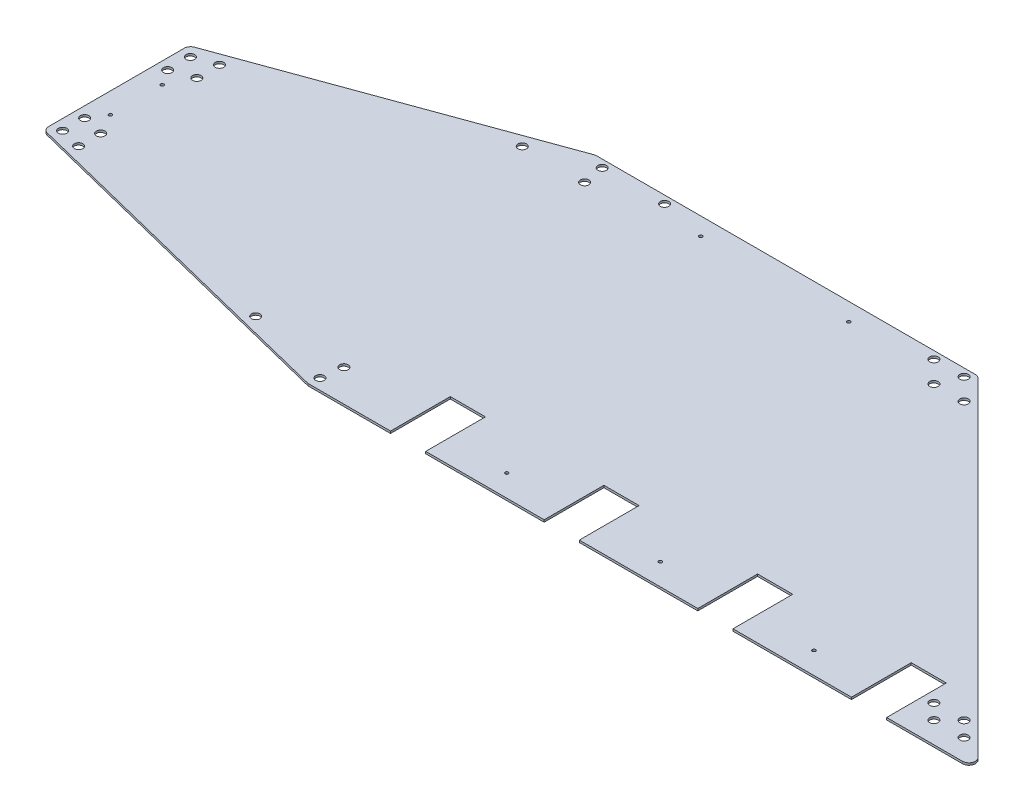
SolidWorks part; units mm, degrees
material "PC High Viscosity"
ref_plane "Front Plane" through (0, 0, 0) normal (0, 0, 1) x (1, 0, 0)
ref_plane "Top Plane" through (0, 0, 0) normal (0, 1, 0) x (1, 0, 0)
ref_plane "Right Plane" through (0, 0, 0) normal (1, 0, 0) x (0, 0, -1)
sketch "Sketch2" plane through (0, 0, 0) normal (0, 1, 0) x (1, 0, 0)
  line L5 (993.5568, 0) -> (0.4168, 0) construction
  line L6 (-516.6797, 128.8227) -> (-1.1348, 0.2829)
  line L7 (1.1695, 0) -> (973.9292, 0)
  line L8 (491.7144, 505.2102) -> (980.6644, 16.2602)
  line L9 (-78.5666, 508) -> (484.9792, 508)
  line L10 (-81.8243, 507.4256) -> (-517.6331, 348.8041)
  line L11 (-523.9004, 339.8536) -> (-523.9004, 138.0648)
  line L36 (122.8448, 0) -> (122.8448, 88.9)
  line L37 (122.8448, 88.9) -> (175.1688, 88.9)
  line L38 (175.1688, 0) -> (175.1688, 88.9)
  line L49 (351.4448, 0) -> (351.4448, 88.9)
  line L50 (351.4448, 88.9) -> (403.7688, 88.9)
  line L51 (403.7688, 0) -> (403.7688, 88.9)
  line L57 (580.0448, 0) -> (580.0448, 88.9)
  line L58 (580.0448, 88.9) -> (632.3688, 88.9)
  line L59 (632.3688, 0) -> (632.3688, 88.9)
  line L61 (808.6448, 0) -> (808.6448, 88.9)
  line L62 (808.6448, 88.9) -> (860.9688, 88.9)
  line L63 (860.9688, 0) -> (860.9688, 88.9)
  arc A0 (-517.6331, 348.8041) -> (-523.9004, 339.8536) centre (-514.3754, 339.8536) ccw
  arc A1 (-523.9004, 138.0648) -> (-516.6797, 128.8227) centre (-514.3754, 138.0648) ccw
  arc A2 (-1.1348, 0.2829) -> (1.1695, 0) centre (1.1695, 9.525) ccw
  arc A3 (980.6644, 16.2602) -> (973.9292, 0) centre (973.9292, 9.525) cw
  arc A4 (491.7144, 505.2102) -> (484.9792, 508) centre (484.9792, 498.475) ccw
  arc A5 (-81.8243, 507.4256) -> (-78.5666, 508) centre (-78.5666, 498.475) cw
  circle A6 centre (133.2169, 15.875) radius 7.62
  circle A7 centre (5.8746, 47.625) radius 6.35
  circle A8 centre (1.9762, 15.875) radius 6.35
  circle A9 centre (-125.3661, 47.625) radius 6.35
  circle A10 centre (-508.0254, 175.7547) radius 6.35
  circle A11 centre (-508.0254, 143.0327) radius 6.35
  circle A12 centre (-476.2754, 167.8385) radius 6.35
  circle A13 centre (-476.2754, 135.1165) radius 6.35
  circle A14 centre (-508.0254, 333.1213) radius 6.35
  circle A15 centre (-476.2754, 344.6773) radius 6.35
  circle A16 centre (-476.2754, 310.8897) radius 6.35
  circle A17 centre (-508.0254, 299.3336) radius 6.35
  circle A18 centre (-146.0386, 464.8731) radius 6.35
  circle A19 centre (-58.8062, 496.6231) radius 6.35
  circle A20 centre (-53.2079, 464.8731) radius 6.35
  circle A21 centre (34.0246, 496.6231) radius 6.35
  circle A22 centre (434.692, 496.623) radius 6.35
  circle A23 centre (466.4419, 464.873) radius 6.35
  circle A24 centre (479.5932, 496.623) radius 6.35
  circle A25 centre (511.3432, 464.873) radius 6.35
  circle A26 centre (877.3398, 53.975) radius 6.35
  circle A27 centre (922.2411, 53.975) radius 6.35
  circle A28 centre (899.5648, 31.75) radius 6.35
  circle A29 centre (944.4661, 31.75) radius 6.35
  circle A31 centre (322.9287, 481.637) radius 2.4575
  circle A32 centre (263.3068, 32.385) radius 2.4575
  circle A33 centre (491.9068, 32.385) radius 2.4575
  circle A34 centre (720.5068, 32.385) radius 2.4575
  circle A35 centre (-493.0394, 276.2907) radius 2.4574
  circle A36 centre (-493.0394, 199.0909) radius 2.4574
  circle A37 centre (102.7505, 481.637) radius 2.4575
  point P8 (-523.9004, 346.523)
  point P18 (-523.9004, 130.623)
  point P21 (0, 0)
  point P24 (996.9246, 0)
  dimension "D9" = 9.525
  dimension "D11" = 121.6753
  dimension "D12" = 52.324
  dimension "D13" = 176.276
  dimension "D14" = 176.276
  dimension "D15" = 176.276
  dimension "D16" = 220.1782
  dimension "D39" = 12.7
  dimension "D45" = 15.24
  dimension "D35" = 4.9149
  dimension "D51" = 4.9149
  dimension "D53" = 4.9149
  dimension "D1" = 523.9004
  dimension "D2" = 508
  dimension "D3" = 1520.825
  dimension "D4" = 166
  dimension "D5" = 160
  dimension "D6" = 110
  dimension "D7" = 215.9
  dimension "D8" = 45
  dimension "D10" = 531.3276
  dimension "D24" = 88.9
  dimension "D25" = 199.0909
  dimension "D29" = 77.1998
  dimension "D30" = 88.9
  dimension "D31" = 88.9
  dimension "D32" = 88.9
extrude "Boss-Extrude1" add sketch "Sketch2" along normal blind 3.175
fillet "Fillet1" [suppressed] radius 3.175
sketch "Sketch6" plane through (0, 3.175, 0) normal (0, 1, 0) x (1, 0, 0)
  line L0 (-22.6592, 431.8127) -> (-22.6592, 406.4127) construction
  line L1 (-9.9592, 431.8127) -> (-9.9592, 406.4127)
  line L2 (-35.3592, 431.8127) -> (-35.3592, 406.4127)
  line L3 (-102.0342, 431.8127) -> (-102.0342, 406.4127) construction
  line L4 (-89.3342, 431.8127) -> (-89.3342, 406.4127)
  line L5 (-114.7342, 431.8127) -> (-114.7342, 406.4127)
  line L6 (-22.6592, 273.0627) -> (-22.6592, 247.6627) construction
  line L7 (-9.9592, 273.0627) -> (-9.9592, 247.6627)
  line L8 (-35.3592, 273.0627) -> (-35.3592, 247.6627)
  line L9 (-102.0342, 273.0627) -> (-102.0342, 247.6627) construction
  line L10 (-89.3342, 273.0627) -> (-89.3342, 247.6627)
  line L11 (-114.7342, 273.0627) -> (-114.7342, 247.6627)
  line L12 (-22.6592, 114.3127) -> (-22.6592, 88.9127) construction
  line L13 (-9.9592, 114.3127) -> (-9.9592, 88.9127)
  line L14 (-35.3592, 114.3127) -> (-35.3592, 88.9127)
  line L15 (-102.0342, 114.3127) -> (-102.0342, 88.9127) construction
  line L16 (-89.3342, 114.3127) -> (-89.3342, 88.9127)
  line L17 (-114.7342, 114.3127) -> (-114.7342, 88.9127)
  arc A0 (-9.9592, 431.8127) -> (-35.3592, 431.8127) centre (-22.6592, 431.8127) ccw
  arc A1 (-35.3592, 406.4127) -> (-9.9592, 406.4127) centre (-22.6592, 406.4127) ccw
  arc A2 (-89.3342, 431.8127) -> (-114.7342, 431.8127) centre (-102.0342, 431.8127) ccw
  arc A3 (-114.7342, 406.4127) -> (-89.3342, 406.4127) centre (-102.0342, 406.4127) ccw
  arc A4 (-9.9592, 273.0627) -> (-35.3592, 273.0627) centre (-22.6592, 273.0627) ccw
  arc A5 (-35.3592, 247.6627) -> (-9.9592, 247.6627) centre (-22.6592, 247.6627) ccw
  arc A6 (-89.3342, 273.0627) -> (-114.7342, 273.0627) centre (-102.0342, 273.0627) ccw
  arc A7 (-114.7342, 247.6627) -> (-89.3342, 247.6627) centre (-102.0342, 247.6627) ccw
  arc A8 (-9.9592, 114.3127) -> (-35.3592, 114.3127) centre (-22.6592, 114.3127) ccw
  arc A9 (-35.3592, 88.9127) -> (-9.9592, 88.9127) centre (-22.6592, 88.9127) ccw
  arc A10 (-89.3342, 114.3127) -> (-114.7342, 114.3127) centre (-102.0342, 114.3127) ccw
  arc A11 (-114.7342, 88.9127) -> (-89.3342, 88.9127) centre (-102.0342, 88.9127) ccw
  point P1 (-76.6342, 419.1127)
  point P2 (-48.0592, 260.3627)
  point P3 (-76.6342, 260.3627)
  point P4 (-76.6342, 101.6127)
  point P5 (-48.0592, 101.6127)
  point P6 (-48.0592, 419.1127)
  point P8 (-22.6592, 419.1127)
  point P13 (-102.0342, 419.1127)
  point P24 (-22.6592, 260.3627)
  point P31 (-102.0342, 260.3627)
  point P38 (-22.6592, 101.6127)
  point P45 (-102.0342, 101.6127)
  dimension "D1" = 25.4
  dimension "D2" = 25.4
  dimension "D3" = 12.7
  dimension "D5" = 12.7
extrude "Cut-Extrude1" [suppressed] cut sketch "Sketch6" against normal blind 6.35
hole_wizard "1/4 (0.25) Diameter Hole1" [suppressed] positions "3DSketch1" profile "Sketch7" hole size "1/4" standard "ANSI Inch"
sketch3d "3DSketch1"
  point P0 (-48.0592, 3.175, -419.1127)
  point P3 (-76.6342, 3.175, -419.1127)
  point P6 (-76.6342, 3.175, -260.3627)
  point P9 (-48.0592, 3.175, -260.3627)
  point P12 (-48.0592, 3.175, -101.6127)
  point P15 (-76.6342, 3.175, -101.6127)
sketch "Sketch7" plane through (-48.0592, 3.175, -419.1127) normal (1, 0, 0) x (0, 0, 1)
  line L0 (0, 0) -> (0, 3.175)
  line L1 (0, 3.175) -> (3.175, 3.175)
  line L2 (3.175, 3.175) -> (3.175, 0)
  line L5 (3.175, 0) -> (0, 0)
  line L11 (0, -6.35) -> (0, 107.95) construction
  dimension "Thru Hole Dia." = 6.35
  dimension "Thru Hole Depth" = 3.175
sketch "Sketch8" plane through (0, 3.175, 0) normal (0, 1, 0) x (1, 0, 0)
  line L0 (-493.0394, 276.2907) -> (-493.0394, 199.0909) construction
  circle A0 centre (-493.0394, 237.6908) radius 22.225
  point P0 (-493.0394, 237.6908)
  dimension "D1" = 44.45
extrude "Cut-Extrude2" [suppressed] cut sketch "Sketch8" against normal through all
sketch "Sketch9" plane through (0, 3.175, 0) normal (0, 1, 0) x (1, 0, 0)
  line L0 (1.1695, 0) -> (122.8448, 0) construction
  line L1 (122.8448, 0) -> (122.8448, 88.9) construction
  line L2 (403.7688, 0) -> (403.7688, 88.9) construction
  line L3 (808.6448, 0) -> (808.6448, 88.9) construction
  point P0 (41.0568, 53.975)
  point P1 (422.0568, 53.975)
  point P2 (803.0568, 53.975)
  dimension "D1" = 53.975
  dimension "D2" = 81.788
  dimension "D3" = 18.288
  dimension "D4" = 5.588
hole_wizard "1/4 (0.25) Diameter Hole2" [suppressed] positions "Sketch10" profile "Sketch11" hole size "1/4" standard "ANSI Inch"
sketch "Sketch10" plane through (0, 3.175, 0) normal (0, 1, 0) x (1, 0, 0)
  point P0 (41.0568, 53.975)
  point P3 (422.0568, 53.975)
  point P6 (803.0568, 53.975)
  point P10 (41.0568, 64.2938)
  point P12 (422.0568, 64.2938)
  point P14 (803.0568, 64.2938)
  dimension "D1" = 10.3187
sketch "Sketch11" plane through (41.0568, 3.175, -53.975) normal (1, 0, 0) x (0, 0, 1)
  line L0 (0, 0) -> (0, 3.175)
  line L1 (0, 3.175) -> (3.175, 3.175)
  line L2 (3.175, 3.175) -> (3.175, 0)
  line L5 (3.175, 0) -> (0, 0)
  line L11 (0, -6.35) -> (0, 107.95) construction
  dimension "Thru Hole Dia." = 6.35
  dimension "Thru Hole Depth" = 3.175
sketch "Sketch12" [suppressed] plane through (0, 3.175, 0) normal (0, 1, 0) x (1, 0, 0)
  line L0 (28.3568, 85.725) -> (53.7568, 85.725) construction
  line L1 (28.3568, 98.425) -> (53.7568, 98.425)
  line L2 (28.3568, 73.025) -> (53.7568, 73.025)
  line L3 (425.2318, 85.725) -> (450.6318, 85.725) construction
  line L4 (425.2318, 98.425) -> (450.6318, 98.425)
  line L5 (425.2318, 73.025) -> (450.6318, 73.025)
  line L6 (764.9568, 85.725) -> (790.3568, 85.725) construction
  line L7 (764.9568, 98.425) -> (790.3568, 98.425)
  line L8 (764.9568, 73.025) -> (790.3568, 73.025)
  arc A0 (28.3568, 98.425) -> (28.3568, 73.025) centre (28.3568, 85.725) ccw
  arc A1 (53.7568, 73.025) -> (53.7568, 98.425) centre (53.7568, 85.725) ccw
  arc A2 (425.2318, 98.425) -> (425.2318, 73.025) centre (425.2318, 85.725) ccw
  arc A3 (450.6318, 73.025) -> (450.6318, 98.425) centre (450.6318, 85.725) ccw
  arc A4 (764.9568, 98.425) -> (764.9568, 73.025) centre (764.9568, 85.725) ccw
  arc A5 (790.3568, 73.025) -> (790.3568, 98.425) centre (790.3568, 85.725) ccw
  circle A6 centre (720.5068, 32.385) radius 2.4575 construction
  circle A7 centre (491.9068, 32.385) radius 2.4575 construction
  circle A8 centre (263.3068, 32.385) radius 2.4575 construction
  circle A9 centre (720.5068, 32.385) radius 2.4575
  circle A10 centre (491.9068, 32.385) radius 2.4575
  circle A11 centre (263.3068, 32.385) radius 2.4575
  circle A12 centre (41.0568, 53.975) radius 3.175 construction
  circle A13 centre (422.0568, 53.975) radius 3.175 construction
  circle A14 centre (803.0568, 53.975) radius 3.175 construction
  circle A15 centre (41.0568, 53.975) radius 3.175
  circle A16 centre (422.0568, 53.975) radius 3.175
  circle A17 centre (803.0568, 53.975) radius 3.175
  point P2 (41.0568, 85.725)
  point P7 (437.9318, 85.725)
  point P14 (777.6568, 85.725)
  dimension "D1" = 12.7
  dimension "D2" = 25.4
  dimension "D3" = 31.75
  dimension "D4" = 12.7
  dimension "D5" = 3.175
extrude "Cut-Extrude3" [suppressed] cut sketch "Sketch12" against normal through all
